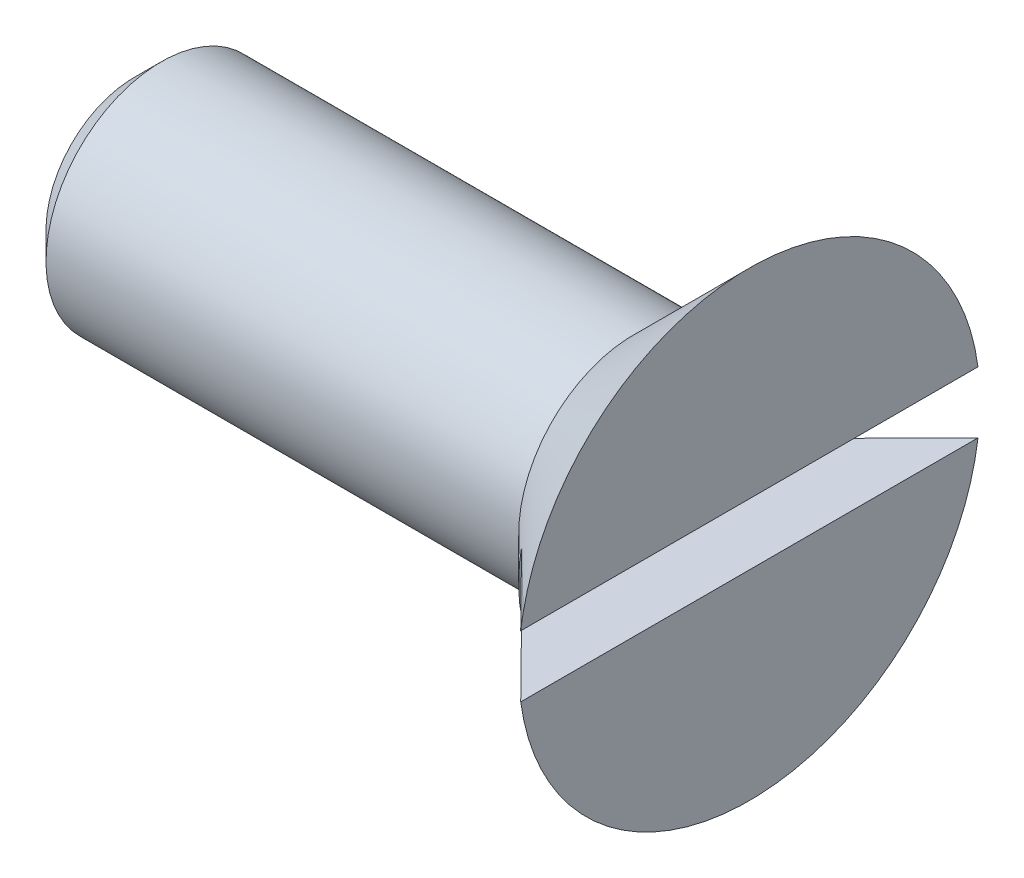
SolidWorks part; units mm, degrees
ref_plane "Front Plane" through (0, 0, 0) normal (0, 0, 1) x (1, 0, 0)
ref_plane "Top Plane" through (0, 0, 0) normal (0, 1, 0) x (1, 0, 0)
ref_plane "Right Plane" through (0, 0, 0) normal (1, 0, 0) x (0, 0, -1)
sketch "Sketch1" plane through (0, 0, 0) normal (0, 0, 1) x (1, 0, 0)
  line L0 (-31.2906, 0) -> (31.2906, 0) construction
  line L1 (6.3829, 0) -> (6.3829, 6)
  line L2 (6.3829, 6) -> (3.3829, 3)
  line L3 (3.3829, 3) -> (-8.91, 3)
  line L4 (-9.6171, 2.2929) -> (-9.6171, 0)
  line L5 (6.3829, 0) -> (-9.6171, 0)
  line L6 (-9.6171, 2.2929) -> (-8.91, 3)
  point P3 (0, 0)
  dimension "D1" = 6
  dimension "D2" = 45
  dimension "D4" = 16
  dimension "D5" = 3
  dimension "D6" = 1
  dimension "D7" = 45
revolve "Revolve1" add sketch "Sketch1" angle 360 about L0
sketch "Sketch2" plane through (0, 0, 0) normal (0, 0, 1) x (1, 0, 0)
  line L0 (-10.3836, 0) -> (4.4829, 0) construction
  line L1 (6.3829, -0.8) -> (4.4829, -0.8)
  line L2 (6.3829, -6) -> (6.3829, 6) construction
  line L3 (4.4829, -0.8) -> (4.4829, 0.8)
  line L5 (6.3829, 0.8) -> (6.3829, -0.8)
  line L6 (6.3829, 0.8) -> (4.4829, 0.8)
  line L7 (4.4829, 0) -> (9.8482, 0) construction
  dimension "D1" = 1.9
extrude "Cut-Extrude1" cut sketch "Sketch2" against normal mid plane 100
